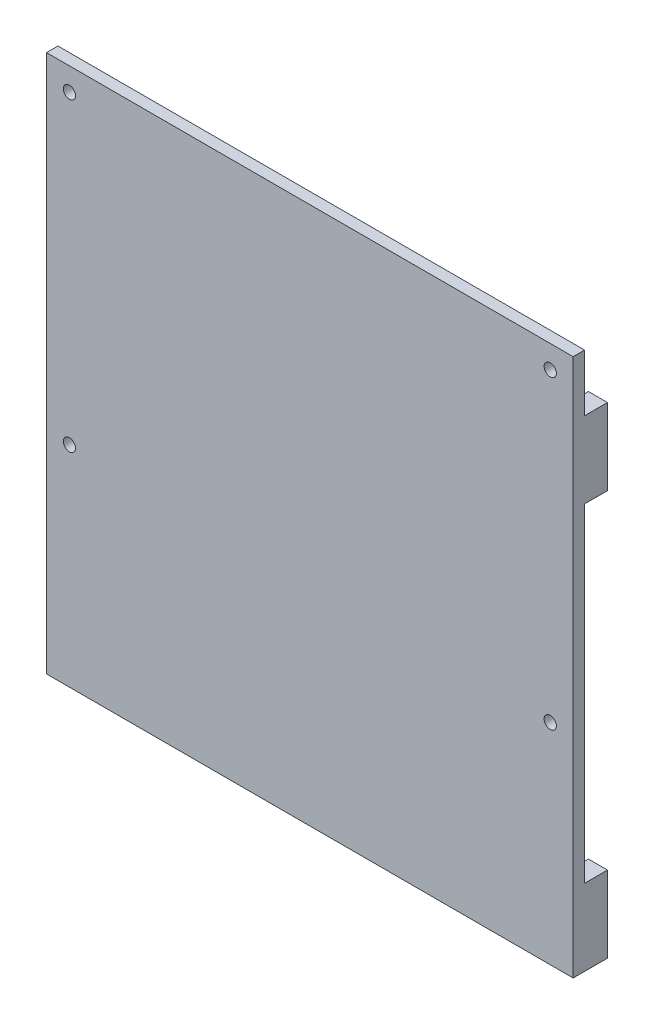
SolidWorks part; units mm, degrees
ref_plane "前视基准面" through (0, 0, 0) normal (0, 0, 1) x (1, 0, 0)
ref_plane "上视基准面" through (0, 0, 0) normal (0, 1, 0) x (1, 0, 0)
ref_plane "右视基准面" through (0, 0, 0) normal (1, 0, 0) x (0, 0, -1)
other "Configuration Table"
sketch "草图1" plane through (0, 0, 0) normal (0, 0, 1) x (1, 0, 0)
  line L1 (-48.1612, 18.3756) -> (77.8388, 18.3756) construction
  line L2 (-48.1612, 18.3756) -> (-48.1612, -61.6244) construction
  line L3 (-48.1612, -61.6244) -> (77.8388, -61.6244) construction
  line L4 (77.8388, 18.3756) -> (77.8388, -61.6244) construction
  line L5 (-54.1612, 24.3756) -> (83.8388, 24.3756)
  line L6 (-54.1612, 24.3756) -> (-54.1612, -116.6244)
  line L7 (-54.1612, -116.6244) -> (83.8388, -116.6244)
  line L8 (83.8388, 24.3756) -> (83.8388, -116.6244)
  circle A0 centre (-48.1612, 18.3756) radius 1.6
  circle A1 centre (77.8388, 18.3756) radius 1.6
  circle A2 centre (-48.1612, -61.6244) radius 1.6
  circle A3 centre (77.8388, -61.6244) radius 1.6
  dimension "D3" = 3.2
  dimension "D1" = 126
  dimension "D2" = 80
  dimension "D4" = 6
  dimension "D5" = 6
  dimension "D6" = 6
  dimension "D7" = 55
extrude "凸台-拉伸1" add sketch "草图1" along normal blind 3
sketch "草图2" plane through (0, 0, 0) normal (0, 0, -1) x (-1, 0, 0)
  line L0 (-83.8388, -116.6244) -> (-83.8388, 24.3756) construction
  line L1 (-83.8388, -96.6244) -> (-78.8388, -96.6244)
  line L2 (-83.8388, -96.6244) -> (-83.8388, -116.6244)
  line L3 (-83.8388, -116.6244) -> (-78.8388, -116.6244)
  line L4 (-78.8388, -96.6244) -> (-78.8388, -116.6244)
  line L5 (54.1612, -116.6244) -> (-83.8388, -116.6244) construction
  line L6 (-14.8388, 24.3756) -> (-14.8388, -116.6244) construction
  line L7 (-83.8388, 9.4652) -> (-78.8388, 9.4652)
  line L8 (-83.8388, 9.4652) -> (-83.8388, -10.5348)
  line L9 (-83.8388, -10.5348) -> (-78.8388, -10.5348)
  line L10 (-78.8388, 9.4652) -> (-78.8388, -10.5348)
  line L11 (-83.8388, 24.3756) -> (54.1612, 24.3756) construction
  line L12 (54.1612, -116.6244) -> (49.1612, -116.6244)
  line L13 (49.1612, -96.6244) -> (49.1612, -116.6244)
  line L14 (54.1612, -96.6244) -> (49.1612, -96.6244)
  line L15 (54.1612, -96.6244) -> (54.1612, -116.6244)
  line L16 (54.1612, -10.5348) -> (49.1612, -10.5348)
  line L17 (49.1612, 9.4652) -> (49.1612, -10.5348)
  line L18 (54.1612, 9.4652) -> (49.1612, 9.4652)
  line L19 (54.1612, 9.4652) -> (54.1612, -10.5348)
  dimension "D1" = 5
  dimension "D2" = 5
  dimension "D3" = 20
  dimension "D4" = 20
extrude "凸台-拉伸2" add sketch "草图2" along normal blind 6
